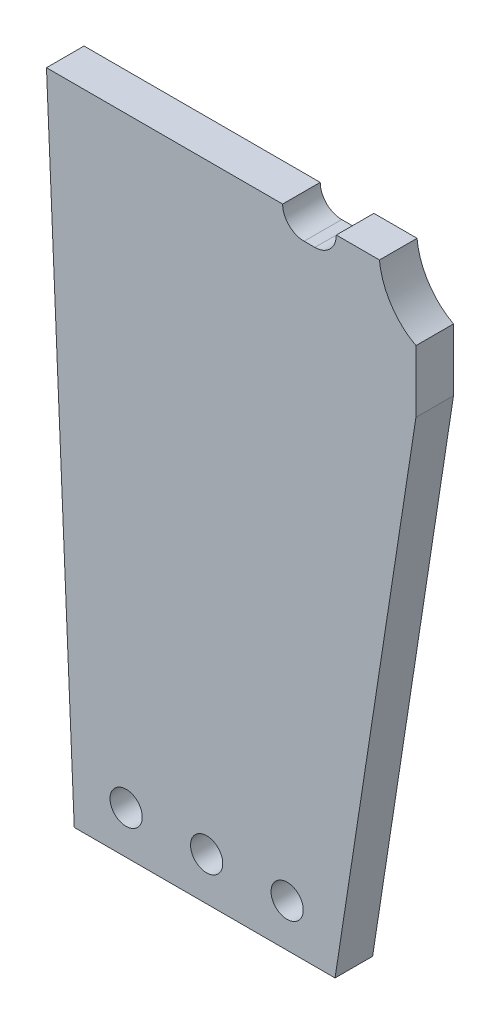
SolidWorks part; units mm, degrees
ref_plane "Front Plane" through (0, 0, 0) normal (0, 0, 1) x (1, 0, 0)
ref_plane "Top Plane" through (0, 0, 0) normal (0, 1, 0) x (1, 0, 0)
ref_plane "Right Plane" through (0, 0, 0) normal (1, 0, 0) x (0, 0, -1)
sketch "Sketch1" plane through (0, 0, 0) normal (0, 0, 1) x (1, 0, 0)
  line L0 (0, 20) -> (0, -305) construction
  line L1 (-22, -50) -> (22, -50)
  line L2 (-22, -50) -> (-11, -305)
  line L3 (-11, -305) -> (0, -305) construction
  line L4 (0, -305) -> (11, -305) construction
  line L5 (11, -305) -> (46.8389, -72)
  line L6 (46.8389, -72) -> (46.8389, -60.4217)
  line L7 (28, -54) -> (26, -54) construction
  line L8 (28, -54) -> (26, -54)
  line L9 (32, -50) -> (40.0462, -50)
  arc A0 (-11, -305) -> (11, -305) centre (0, -304.5255) ccw
  circle A1 centre (0, -305) radius 4.5
  arc A2 (28, -54) -> (32, -50) centre (28, -50) ccw construction
  arc A3 (22, -50) -> (26, -54) centre (26, -50) ccw construction
  arc A4 (28, -54) -> (32, -50) centre (28, -50) ccw
  arc A5 (22, -50) -> (26, -54) centre (26, -50) ccw
  spline S0 degree 3 poles (-413.0418, 1879.7645) (276.2189, -125.2168) (30.346, -91.1298) (48.299, -8.7941) (181.3198, -41.9405) (-1634.2989, 1047.346) knots -3.829034 -3.829034 -3.829034 -3.829034 0.434931 0.661678 4.201483 4.201483 4.201483 4.201483 only from (46.8389, -60.4217) to (46.8389, -34.5209) construction
  spline S1 degree 3 poles (46.8389, -60.4217) (42.9828, -58.3958) (38.9062, -51.8713) (41.1386, -41.633) (45.189, -37.4611) (46.8389, -34.5209) knots 0 0 0 0 0.434931 0.661678 0.998582 0.998582 0.998582 0.998582
  dimension "D2" = 9
  dimension "D3" = 11
  dimension "D1" = 325
extrude "Boss-Extrude1" add sketch "Sketch1" along normal blind 7 contours L6 S1 L1 L2 A0 L5
sketch "Sketch2" plane through (0, 0, 7) normal (0, 0, 1) x (1, 0, 0)
  line L0 (-22, -50) -> (22, -50) construction
  line L1 (-156.4762, -170) -> (246.4423, -170)
  line L2 (-156.4762, -170) -> (-156.4762, -382.6459)
  line L3 (-156.4762, -382.6459) -> (246.4423, -382.6459)
  line L4 (246.4423, -170) -> (246.4423, -382.6459)
  dimension "D1" = 120
extrude "Cut-Extrude1" cut sketch "Sketch2" against normal blind 30
sketch "Sketch3" plane through (0, 0, 7) normal (0, 0, 1) x (1, 0, 0)
  line L0 (-17.1686, -162) -> (32.9955, -162) construction
  line L1 (-22, -50) -> (-16.8235, -170) construction
  line L2 (31.765, -170) -> (46.8389, -72) construction
  line L3 (31.765, -170) -> (-16.8235, -170) construction
  circle A0 centre (-7.1593, -162) radius 3
  circle A1 centre (7.8407, -162) radius 3
  circle A2 centre (22.8407, -162) radius 3
  dimension "D2" = 6
  dimension "D3" = 10
  dimension "D5" = 15
  dimension "D1" = 8
  dimension "D4" = 3
extrude "Cut-Extrude2" cut sketch "Sketch3" against normal through all
